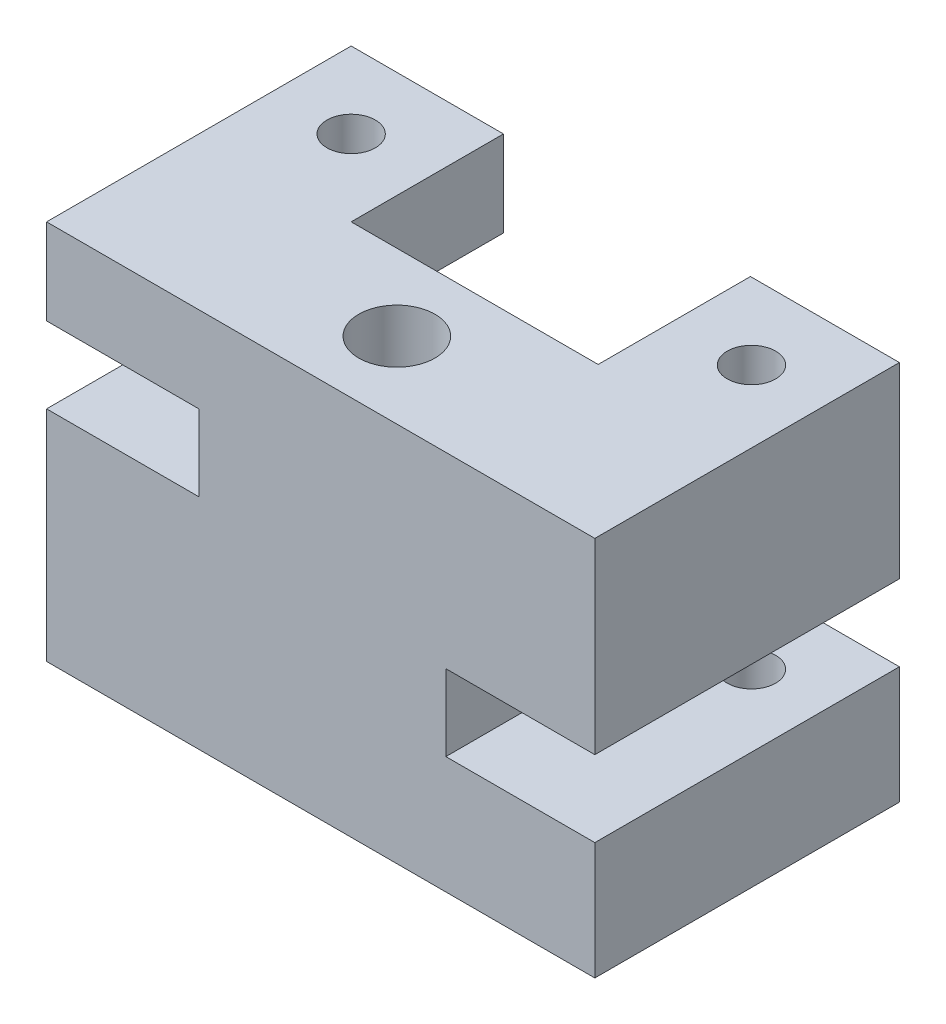
SolidWorks part; units mm, degrees
material "1060 Alloy"
ref_plane "Front Plane" through (0, 0, 0) normal (0, 0, 1) x (1, 0, 0)
ref_plane "Top Plane" through (0, 0, 0) normal (0, 1, 0) x (1, 0, 0)
ref_plane "Right Plane" through (0, 0, 0) normal (1, 0, 0) x (0, 0, -1)
sketch "Sketch1" plane through (0, 0, 0) normal (0, 0, 1) x (1, 0, 0)
  line L0 (-54, 34.4017) -> (54, 34.4017)
  line L5 (54, 34.4017) -> (54, -2.5)
  line L6 (54, -2.5) -> (24.6547, -2.5)
  line L7 (24.6547, -2.5) -> (24.6547, -17.5)
  line L8 (24.6547, -17.5) -> (54, -17.5)
  line L9 (54, -17.5) -> (54, -40.5983)
  line L10 (54, -40.5983) -> (-54, -40.5983)
  line L11 (-54, -40.5983) -> (-54, 2.5)
  line L12 (-54, 2.5) -> (-24, 2.5)
  line L13 (-24, 2.5) -> (-24, 17.5)
  line L14 (-24, 17.5) -> (-54, 17.5)
  line L15 (-54, 17.5) -> (-54, 34.4017)
  line L17 (-39, 17.5) -> (-39, 2.5) construction
  point P5 (-24, 8.8122)
  point P13 (-24, -5.6181)
  point P14 (24.6547, -22.0465)
  point P16 (-24, 7.4802)
  point P17 (0, 34.4017)
  point P18 (0, -40.5983)
  dimension "D5" = 15
  dimension "D1" = 30
  dimension "D2" = 39
  dimension "D6" = 15
  dimension "D3" = 5
  dimension "D4" = 2.5
extrude "Boss-Extrude1" add sketch "Sketch1" along normal blind 30
sketch "Sketch3" plane through (0, 34.4017, 0) normal (0, 1, 0) x (1, 0, 0)
  circle A0 centre (0, -15) radius 7.5
  dimension "D2" = 15
  dimension "D1" = 15
extrude "Cut-Extrude3" cut sketch "Sketch3" against normal through all contours A0
sketch "Sketch4" plane through (0, 0, 0) normal (0, 0, -1) x (-1, 0, 0)
  line L1 (-54, 34.4017) -> (-24.6547, 34.4017)
  line L2 (-54, 34.4017) -> (-54, -2.5)
  line L3 (-54, -2.5) -> (-24.6547, -2.5)
  line L4 (-24.6547, 34.4017) -> (-24.6547, -2.5)
  line L5 (-54, -17.5) -> (-24.6547, -17.5)
  line L6 (-54, -17.5) -> (-54, -40.5983)
  line L7 (-54, -40.5983) -> (-24.6547, -40.5983)
  line L8 (-24.6547, -17.5) -> (-24.6547, -40.5983)
  line L9 (-54, 34.4017) -> (54, 34.4017) construction
  line L10 (24, 2.5) -> (54, 2.5)
  line L11 (24, 2.5) -> (24, -40.5983)
  line L12 (24, -40.5983) -> (54, -40.5983)
  line L13 (54, 2.5) -> (54, -40.5983)
  line L14 (54, 17.5) -> (24, 17.5)
  line L15 (54, 17.5) -> (54, 34.4017)
  line L16 (54, 34.4017) -> (24, 34.4017)
  line L17 (24, 17.5) -> (24, 34.4017)
  line L19 (54, -40.5983) -> (-54, -40.5983) construction
  point P11 (-24.6547, -17.5)
  point P12 (-24.6547, -40.5983)
  point P26 (-30.9017, -17.5)
  point P30 (24, 17.5)
extrude "Boss-Extrude2" add sketch "Sketch4" along normal blind 30
sketch "Sketch2" plane through (0, 34.4017, 0) normal (0, 1, 0) x (1, 0, 0)
  line L0 (-39.8532, 15) -> (39.8532, 15) construction
  line L2 (24.6547, 30) -> (54, 30) construction
  circle A1 centre (39.8532, 15) radius 4.7625
  dimension "D2" = 9.525
  dimension "D1" = 15
extrude "Cut-Extrude2" cut sketch "Sketch2" against normal offset from surface (61.9017 mm away) 10 up to face at (36.3928, -17.5, 0) offset beyond the face yes
sketch "Sketch5" plane through (0, 34.4017, 0) normal (0, 1, 0) x (1, 0, 0)
  line L0 (-39, 15) -> (39.8532, 15) construction
  line L1 (-39, 15) -> (-39, 30) construction
  line L2 (-54, 30) -> (-24, 30) construction
  circle A0 centre (-39, 15) radius 4.7625
  circle A1 centre (39.8532, 15) radius 4.7625 construction
extrude "Cut-Extrude4" cut sketch "Sketch5" against normal offset from surface (41.9017 mm away) 10 up to face at (-36, 2.5, 0) offset beyond the face yes
equation "\"D4@Sketch1\"=\"D3@Sketch1\"/2"
